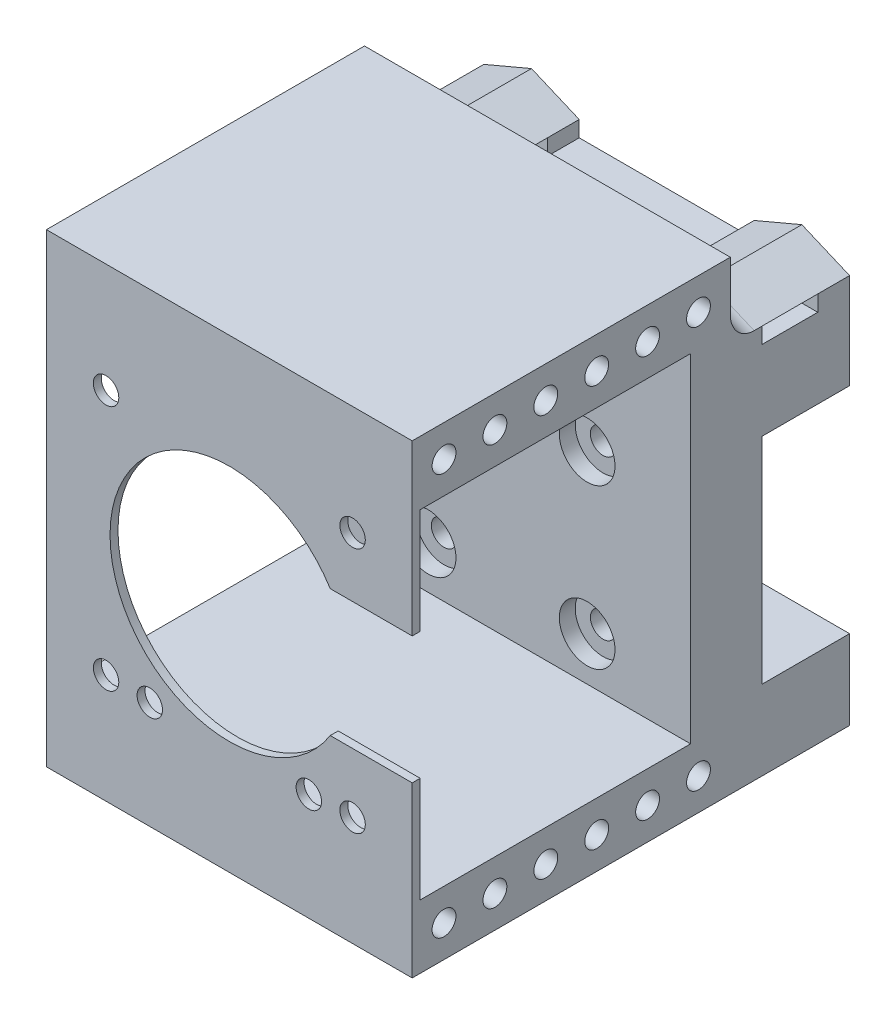
SolidWorks part; units mm, degrees
ref_plane "Front Plane" through (0, 0, 0) normal (0, 0, 1) x (1, 0, 0)
ref_plane "Top Plane" through (0, 0, 0) normal (0, 1, 0) x (1, 0, 0)
ref_plane "Right Plane" through (0, 0, 0) normal (1, 0, 0) x (0, 0, -1)
sketch "Sketch1" plane through (0, 0, 0) normal (0, 0, 1) x (1, 0, 0)
  line L5 (-23, -23.5) -> (23, -23.5)
  line L6 (-23, -23.5) -> (-23, 23.5)
  line L7 (-23, 23.5) -> (23, 23.5)
  line L8 (23, -23.5) -> (23, 23.5)
  line L9 (-23, -23.5) -> (23, 23.5) construction
  line L10 (-23, 23.5) -> (23, -23.5) construction
  point P0 (0, 0)
  dimension "D1" = 46
  dimension "D2" = 47
extrude "Boss-Extrude1" add sketch "Sketch1" along normal blind 9
sketch "Sketch3" plane through (0, 0, 0) normal (0, 0, 1) x (1, 0, 0)
  line L0 (23, -23.5) -> (23, 23.5) construction
  line L1 (23, 23.5) -> (-23, 23.5)
  line L2 (23, 23.5) -> (23, 13.5)
  line L3 (23, 13.5) -> (-23, 13.5)
  line L4 (-23, 23.5) -> (-23, 13.5)
  line L5 (-23, 23.5) -> (-23, -23.5) construction
  line L7 (23, -23.5) -> (-23, -23.5)
  line L8 (23, -23.5) -> (23, -13.5)
  line L9 (23, -13.5) -> (-23, -13.5)
  line L10 (-23, -23.5) -> (-23, -13.5)
  dimension "D1" = 13.5
  dimension "D2" = 10
  dimension "D3" = 10
extrude "Boss-Extrude2" add sketch "Sketch3" against normal blind 11
sketch "Sketch4" plane through (0, 0, 0) normal (0, 0, 1) x (1, 0, 0)
  line L0 (23, 23.5) -> (-23, 23.5) construction
  line L1 (-23, 23.5) -> (-23, -23.5) construction
  circle A0 centre (-17, 18.5) radius 2.15
  circle A1 centre (17, 18.5) radius 2.15
  circle A2 centre (-17, -18.5) radius 2.15
  circle A3 centre (17, -18.5) radius 2.15
  dimension "D1" = 4.3
  dimension "D5" = 2
  dimension "D2" = 5
  dimension "D3" = 6
  dimension "D6" = 34
  dimension "D7" = 37
  dimension "D4" = 2
extrude "Cut-Extrude2" [suppressed] cut sketch "Sketch4" against normal through all both and the other way through all
sketch "Sketch7" plane through (0, 0, -11) normal (0, 0, -1) x (-1, 0, 0)
  line L0 (0, 23.5) -> (0, 39.2593) construction
  line L4 (-23, 23.5) -> (23, 23.5) construction
  line L5 (-23, 23.5) -> (-11, 23.5)
  line L6 (-23, 23.5) -> (-23, 25.5)
  line L8 (-11, 23.5) -> (-11, 25.5)
  line L9 (-23, 25.5) -> (-17, 28.0449)
  line L14 (-17, 28.0449) -> (-11, 25.5)
  line L15 (17, 28.0449) -> (11, 25.5)
  line L16 (23, 25.5) -> (17, 28.0449)
  line L17 (11, 23.5) -> (11, 25.5)
  line L18 (23, 23.5) -> (23, 25.5)
  line L19 (23, 23.5) -> (11, 23.5)
  line L20 (-17, 23.5) -> (-17, 30.4296) construction
  dimension "D1" = 2
  dimension "D2" = 2
extrude "Boss-Extrude5" add sketch "Sketch7" against normal blind 15
sketch "Sketch8" plane through (0, 0, 0) normal (1, 0, 0) x (0, 0, -1)
  line L0 (-4, 23.5) -> (11, 23.5) construction
  line L1 (7, 23.5) -> (0, 23.5)
  line L2 (7, 23.5) -> (7, 25.5)
  line L3 (7, 25.5) -> (0, 25.5)
  line L4 (0, 23.5) -> (0, 25.5)
  line L6 (11, 23.5) -> (11, 25.5) construction
  dimension "D1" = 4
  dimension "D2" = 7
extrude "Cut-Extrude3" cut sketch "Sketch8" against normal through all both and the other way through all
sketch "Sketch10" [suppressed] plane through (0, 0, -11) normal (0, 0, -1) x (-1, 0, 0)
  circle A0 centre (-17, -18.5) radius 3.2
  circle A1 centre (17, -18.5) radius 3.2
  circle A2 centre (17, 18.5) radius 3.2
  circle A3 centre (-17, 18.5) radius 3.2
  dimension "D1" = 6.4
extrude "Cut-Extrude5" [suppressed] cut sketch "Sketch10" against normal blind 13
ref_plane "Plane1" through (0, 0, 9) normal (0, 0, 1) x (1, 0, 0)
sketch "Sketch11" plane through (0, 0, 9) normal (0, 0, 1) x (1, 0, 0)
  line L0 (23, -23.5) -> (23, 23.5) construction
  line L1 (-23, -23.5) -> (23, -23.5)
  line L2 (-23, -23.5) -> (-23, -15.5)
  line L3 (-23, -15.5) -> (23, -15.5)
  line L4 (23, -23.5) -> (23, -15.5)
  line L5 (-23, 23.5) -> (-23, -23.5) construction
  line L6 (-23, 27) -> (23, 27)
  line L7 (-23, 27) -> (-23, 35)
  line L8 (-23, 35) -> (23, 35)
  line L9 (23, 27) -> (23, 35)
  dimension "D1" = 8
  dimension "D2" = 8
  dimension "D3" = 42.5
extrude "Boss-Extrude6" add sketch "Sketch11" along normal blind 34
ref_plane "Plane2" through (0, 0, 43) normal (0, 0, 1) x (1, 0, 0)
sketch "Sketch12" plane through (0, 0, 43) normal (0, 0, 1) x (1, 0, 0)
  line L1 (-23, 35) -> (23, 35)
  line L2 (-23, 35) -> (-23, -23.5)
  line L3 (-23, -23.5) -> (23, -23.5)
  line L4 (23, 35) -> (23, -23.5)
extrude "Boss-Extrude7" add sketch "Sketch12" along normal blind 1
sketch "Sketch13" plane through (0, 0, 44) normal (0, 0, 1) x (1, 0, 0)
  line L0 (-23, -23.5) -> (23, -23.5) construction
  line L1 (23, -23.5) -> (23, 35) construction
  line L2 (-15.5, -9.75) -> (15.5, -9.75) construction
  line L3 (-15.5, -9.75) -> (-15.5, 21.25) construction
  line L4 (-15.5, 21.25) -> (15.5, 21.25) construction
  line L5 (15.5, -9.75) -> (15.5, 21.25) construction
  line L6 (-15.5, -9.75) -> (15.5, 21.25) construction
  line L7 (-15.5, 21.25) -> (15.5, -9.75) construction
  circle A0 centre (0, 5.75) radius 15
  circle A1 centre (-15.5, 21.25) radius 1.6
  circle A2 centre (15.5, 21.25) radius 1.6
  circle A3 centre (15.5, -9.75) radius 1.6
  circle A4 centre (-15.5, -9.75) radius 1.6
  dimension "D1" = 30
  dimension "D6" = 3.2
  dimension "D2" = 29.25
  dimension "D3" = 23
  dimension "D4" = 31
  dimension "D5" = 31
extrude "Cut-Extrude6" cut sketch "Sketch13" against normal up to next
sketch "Sketch14" plane through (0, 23.5, 0) normal (0, 1, 0) x (1, 0, 0)
  line L1 (23, -4) -> (-23, -4)
  line L2 (23, -4) -> (23, -9)
  line L3 (23, -9) -> (-23, -9)
  line L4 (-23, -4) -> (-23, -9)
extrude "Boss-Extrude8" add sketch "Sketch14" along normal up to surface (11.5 mm away) up to face at (0, 35, 26.5)
sketch "Sketch15" plane through (0, 0, 44) normal (0, 0, 1) x (1, 0, 0)
  line L0 (23, -23.5) -> (23, 35) construction
  line L1 (7, -2.248) -> (23, -2.248)
  line L2 (7, -2.248) -> (7, 13.748)
  line L3 (7, 13.748) -> (23, 13.748)
  line L4 (23, -2.248) -> (23, 13.748)
  line L5 (7, -2.248) -> (23, 13.748) construction
  line L6 (7, 13.748) -> (23, -2.248) construction
  circle A0 centre (0, 5.75) radius 15 construction
  point P0 (15, 5.75)
extrude "Cut-Extrude7" cut sketch "Sketch15" against normal blind 3
sketch "Sketch2" plane through (0, 0, 9) normal (0, 0, 1) x (1, 0, 0)
  circle A0 centre (-10, 10) radius 1.6
  circle A3 centre (10, 10) radius 1.6
  circle A4 centre (-10, -10) radius 1.6
  circle A5 centre (10, -10) radius 1.6
  dimension "D1" = 3.2
  dimension "D2" = 10
  dimension "D3" = 10
  dimension "D4" = 2
  dimension "D5" = 2
extrude "Cut-Extrude1" cut sketch "Sketch2" against normal through all both and the other way through all
sketch "Sketch9" plane through (0, 0, 9) normal (0, 0, 1) x (1, 0, 0)
  circle A0 centre (-10, 10) radius 3.5
  circle A1 centre (10, 10) radius 3.5
  circle A2 centre (10, -10) radius 3.5
  circle A3 centre (-10, -10) radius 3.5
  dimension "D1" = 7
extrude "Cut-Extrude4" cut sketch "Sketch9" against normal blind 2
fillet "Fillet1" radius 3 7 edges at (-20, 26.7724, 4) (-14, 26.7724, 4) (-11, 24.5, 4) (11, 24.5, 4) (0, 23.5, 4) (20, 26.7724, 4) (14, 26.7724, 4)
sketch "Sketch17" plane through (-23, 0, 0) normal (-1, 0, 0) x (0, 0, 1)
  line L0 (4, 35) -> (4, 28.7587) construction
  line L1 (44, 35) -> (44, -23.5) construction
  line L2 (44, -23.5) -> (-11, -23.5) construction
  line L4 (44, 35) -> (4, 35) construction
  circle A11 centre (40, -19.5) radius 1.5
  circle A12 centre (33.6, -19.5) radius 1.5
  circle A13 centre (27.2, -19.5) radius 1.5
  circle A14 centre (20.8, -19.5) radius 1.5
  circle A15 centre (14.4, -19.5) radius 1.5
  circle A16 centre (8, -19.5) radius 1.5
  circle A20 centre (33.6, 31) radius 1.5
  circle A21 centre (27.2, 31) radius 1.5
  circle A22 centre (20.8, 31) radius 1.5
  circle A23 centre (14.4, 31) radius 1.5
  circle A24 centre (8, 31) radius 1.5
  circle A28 centre (40, 31) radius 1.5
  dimension "D3" = 3
  dimension "D6" = 4
  dimension "D1" = 4
  dimension "D2" = 4
  dimension "D7" = 4
  dimension "D4" = 6
  dimension "D5" = 2
extrude "Cut-Extrude8" cut sketch "Sketch17" against normal through all
sketch "Sketch20" plane through (0, 0, -11) normal (0, 0, -1) x (-1, 0, 0)
  line L0 (-23, -23.5) -> (-23, -13.5) construction
  line L1 (23, -23.5) -> (-23, -23.5) construction
  line L2 (23, -13.5) -> (23, -23.5) construction
  line L3 (23, 13.5) -> (-23, 13.5) construction
  circle A0 centre (-19, -18.5) radius 1.5
  circle A1 centre (-12.6667, -18.5) radius 1.5
  circle A2 centre (-6.3333, -18.5) radius 1.5
  circle A3 centre (0, -18.5) radius 1.5
  circle A4 centre (6.3333, -18.5) radius 1.5
  circle A5 centre (12.6667, -18.5) radius 1.5
  circle A6 centre (19, -18.5) radius 1.5
  circle A7 centre (-19, 18.5) radius 1.5
  circle A8 centre (-12.6667, 18.5) radius 1.5
  circle A9 centre (-6.3333, 18.5) radius 1.5
  circle A10 centre (0, 18.5) radius 1.5
  circle A11 centre (6.3333, 18.5) radius 1.5
  circle A12 centre (12.6667, 18.5) radius 1.5
  circle A13 centre (19, 18.5) radius 1.5
  dimension "D1" = 3
  dimension "D2" = 4
  dimension "D3" = 5
  dimension "D5" = 4
  dimension "D7" = 5
  dimension "D4" = 7
  dimension "D6" = 2
extrude "Cut-Extrude10" cut sketch "Sketch20" against normal blind 10
